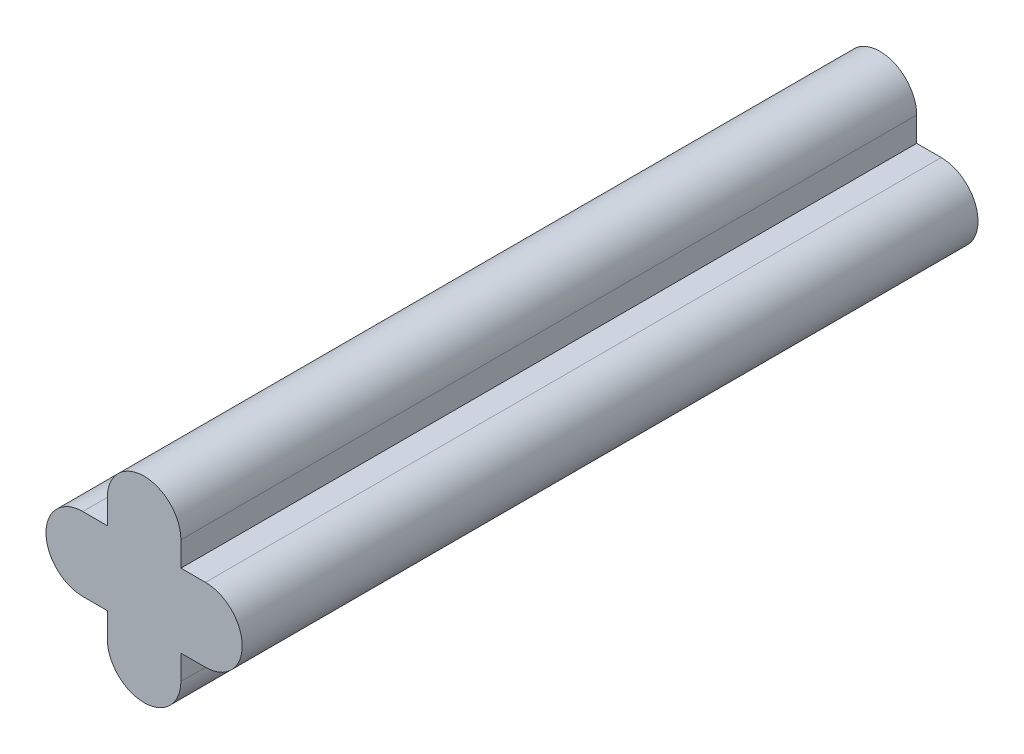
SolidWorks part; units mm, degrees
ref_plane "Front Plane" through (0, 0, 0) normal (0, 0, 1) x (1, 0, 0)
ref_plane "Top Plane" through (0, 0, 0) normal (0, 1, 0) x (1, 0, 0)
ref_plane "Right Plane" through (0, 0, 0) normal (1, 0, 0) x (0, 0, -1)
sketch "Sketch1" plane through (0, 0, 0) normal (0, 0, 1) x (1, 0, 0)
  line L0 (-2.5, 0) -> (2.5, 0) construction
  line L1 (-2.5, 1.5) -> (-1.5, 1.5)
  line L2 (-2.5, -1.5) -> (-1.5, -1.5)
  line L3 (0, 2.5) -> (0, -2.5) construction
  line L4 (1.5, 2.5) -> (1.5, 1.5)
  line L5 (-1.5, 2.5) -> (-1.5, 1.5)
  line L6 (1.5, 1.5) -> (2.5, 1.5)
  line L7 (-1.5, -1.5) -> (-1.5, -2.5)
  line L8 (1.5, -1.5) -> (2.5, -1.5)
  line L9 (1.5, -1.5) -> (1.5, -2.5)
  circle A0 centre (0, 0) radius 4 construction
  arc A1 (-2.5, 1.5) -> (-2.5, -1.5) centre (-2.5, 0) ccw
  arc A2 (2.5, -1.5) -> (2.5, 1.5) centre (2.5, 0) ccw
  arc A3 (1.5, 2.5) -> (-1.5, 2.5) centre (0, 2.5) ccw
  arc A4 (-1.5, -2.5) -> (1.5, -2.5) centre (0, -2.5) ccw
  point P5 (0, 0)
  point P6 (0, 0)
  point P13 (0, 0)
  point P18 (1.5219, 2.4781)
  dimension "D1" = 8
  dimension "D2" = 3
extrude "Boss-Extrude1" add sketch "Sketch1" along normal blind 30
